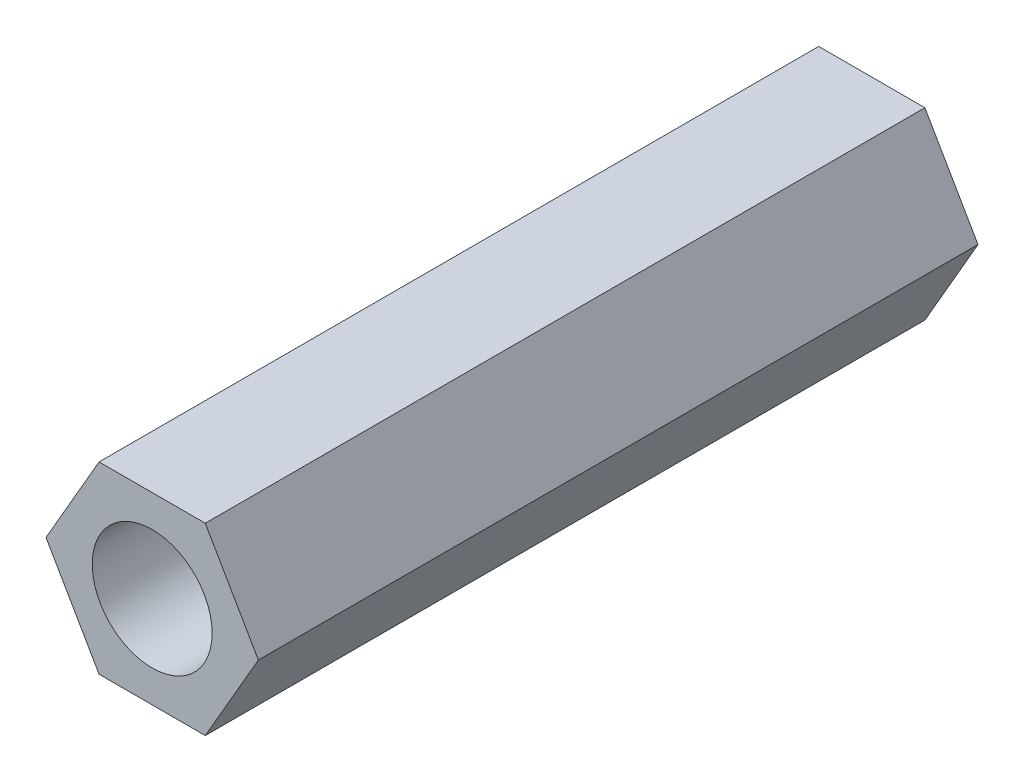
SolidWorks part; units mm, degrees
ref_plane "前视基准面" through (0, 0, 0) normal (0, 0, 1) x (1, 0, 0)
ref_plane "上视基准面" through (0, 0, 0) normal (0, 1, 0) x (1, 0, 0)
ref_plane "右视基准面" through (0, 0, 0) normal (1, 0, 0) x (0, 0, -1)
sketch "草图1" plane through (0, 0, 0) normal (0, 0, 1) x (1, 0, 0)
  line L1 (2.6558, 0) -> (1.3279, 2.3)
  line L2 (1.3279, 2.3) -> (-1.3279, 2.3)
  line L3 (-1.3279, 2.3) -> (-2.6558, 0)
  line L4 (-2.6558, 0) -> (-1.3279, -2.3)
  line L5 (-1.3279, -2.3) -> (1.3279, -2.3)
  line L6 (1.3279, -2.3) -> (2.6558, 0)
  circle A0 centre (0, 0) radius 1.5
  circle A1 centre (0, 0) radius 2.3 construction
  dimension "D1" = 3
  dimension "D2" = 4.6
extrude "凸台-拉伸1" add sketch "草图1" along normal blind 18
